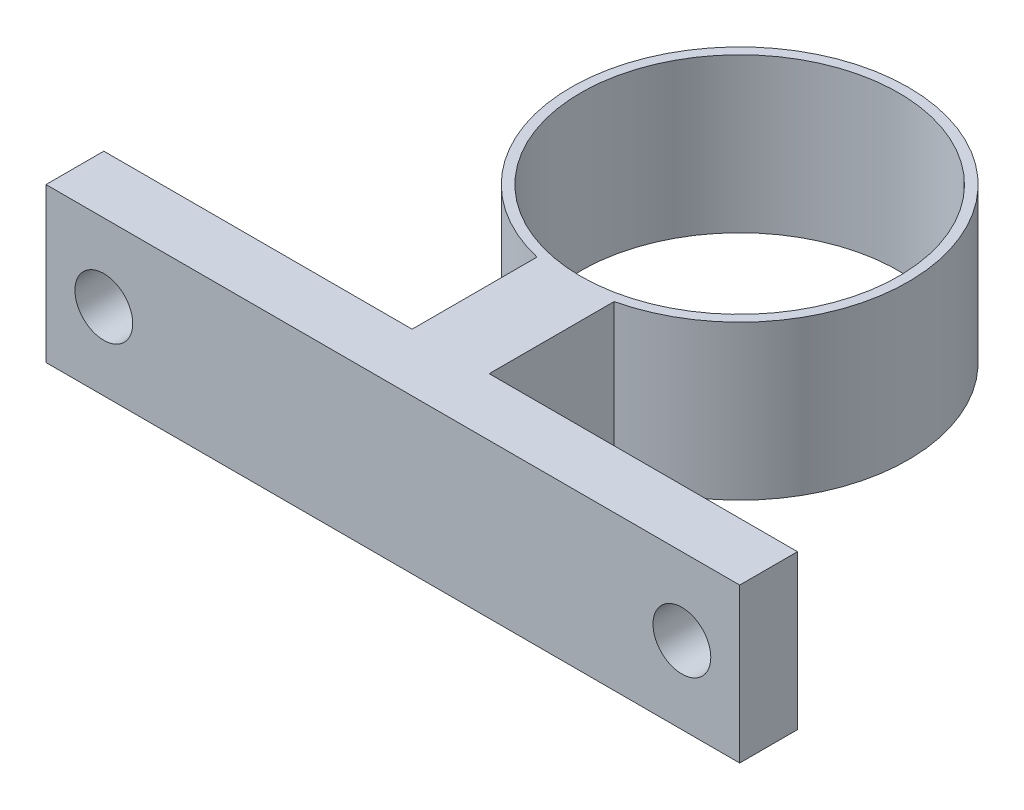
SolidWorks part; units mm, degrees
ref_plane "前视基准面" through (0, 0, 0) normal (0, 0, 1) x (1, 0, 0)
ref_plane "上视基准面" through (0, 0, 0) normal (0, 1, 0) x (1, 0, 0)
ref_plane "右视基准面" through (0, 0, 0) normal (1, 0, 0) x (0, 0, -1)
sketch "草图1" plane through (0, 0, 0) normal (0, 1, 0) x (1, 0, 0)
  circle A0 centre (0, 0) radius 8.25
  circle A1 centre (0, 0) radius 8.75
  dimension "D1" = 16.5
  dimension "D2" = 17.5
extrude "凸台-拉伸2" add sketch "草图1" along normal blind 10
sketch "草图2" plane through (0, 0, 0) normal (0, 1, 0) x (1, 0, 0)
  circle A0 centre (0, 0) radius 8.25
  circle A1 centre (0, 0) radius 2
  dimension "D1" = 4
extrude "凸台-拉伸3" add sketch "草图2" along normal blind 4
sketch "草图3" plane through (0, 0, 0) normal (0, 1, 0) x (1, 0, 0)
  line L0 (-2, 8.5184) -> (2, 8.5184)
  line L1 (-15, 18) -> (-15, 15)
  line L2 (2, 18) -> (15, 18)
  line L3 (-2, 8.5184) -> (-2, 15)
  line L4 (2, 8.5184) -> (2, 15)
  line L5 (-15, 18) -> (-2, 18)
  line L6 (-15, 15) -> (-2, 15)
  line L7 (15, 15) -> (15, 18)
  line L8 (2, 15) -> (15, 15)
  line L9 (2, 18) -> (-2, 18)
  circle A2 centre (0, 0) radius 8.75 construction
  dimension "D1" = 13
  dimension "D2" = 13
  dimension "D3" = 3
  dimension "D4" = 3
extrude "凸台-拉伸4" add sketch "草图3" along normal blind 8
sketch "草图5" plane through (15, 0, 0) normal (1, 0, 0) x (0, 0, -1)
  line L0 (15, 8) -> (18, 8)
  line L1 (15, 8) -> (15, 0)
  line L2 (18, 8) -> (18, 0)
  line L3 (15, 0) -> (18, 0)
  dimension "D1" = 8
extrude "凸台-拉伸5" add sketch "草图5" along normal blind 3
sketch "草图6" plane through (-15, 0, 0) normal (-1, 0, 0) x (0, 0, 1)
  line L0 (-18, 8) -> (-15, 8)
  line L1 (-18, 8) -> (-18, 0)
  line L2 (-15, 8) -> (-15, 0)
  line L3 (-18, 0) -> (-15, 0)
  dimension "D1" = 8
extrude "凸台-拉伸6" add sketch "草图6" along normal blind 3
sketch "草图7" plane through (0, 0, -18) normal (0, 0, -1) x (-1, 0, 0)
  circle A0 centre (-15, 3.754) radius 1.5
  dimension "D2" = 3
extrude "切除-拉伸1" cut sketch "草图7" against normal blind 3
mirror "镜向1" about plane through (0, 0, 0) normal (1, 0, 0) of "切除-拉伸1"
fillet "圆角1" radius 5 2 edges at (2, 4, -8.5184) (-2, 4, -8.5184)
fillet "圆角3" radius 2 2 edges at (-2, 4, -15) (2, 4, -15)
ref_plane "基准面1" through (0, 0, 10) normal (0, 0, 1) x (1, 0, 0)
sketch "草图8" plane through (0, 0, 0) normal (0, 1, 0) x (1, 0, 0)
  circle A0 centre (27.185, 0) radius 8.75
  circle A1 centre (27.185, 0) radius 8.25
  dimension "D1" = 17.5
  dimension "D2" = 16.5
extrude "凸台-拉伸7" add sketch "草图8" along normal blind 8 separate body
sketch "草图9" plane through (0, 0, 0) normal (0, -1, 0) x (1, 0, 0)
  circle A0 centre (27.185, 0) radius 8.25
  circle A1 centre (27.185, 0) radius 6
  dimension "D1" = 12
extrude "凸台-拉伸8" add sketch "草图9" against normal blind 2
sketch "草图10" plane through (0, 0, 0) normal (0, 1, 0) x (1, 0, 0)
  line L1 (27.185, -18) -> (45.185, -18)
  line L2 (27.185, -18) -> (9.185, -18)
  line L3 (9.185, -18) -> (9.185, -14.6639)
  line L4 (9.185, -14.6639) -> (25.185, -14.6639)
  line L5 (45.185, -18) -> (45.185, -14.6639)
  line L6 (45.185, -14.6639) -> (29.185, -14.6639)
  line L7 (25.185, -14.6639) -> (25.185, -8.5184)
  line L8 (25.185, -8.5184) -> (29.185, -8.5184)
  line L9 (29.185, -8.5184) -> (29.185, -14.6639)
  circle A0 centre (27.185, 0) radius 8.75 construction
  dimension "D2" = 18
  dimension "D3" = 18
  dimension "D4" = 16
  dimension "D5" = 16
extrude "凸台-拉伸9" add sketch "草图10" along normal blind 8
sketch "草图11" plane through (0, 0, 18) normal (0, 0, 1) x (1, 0, 0)
  circle A0 centre (12.185, 4) radius 1.5
  circle A1 centre (42.185, 4) radius 1.5
  dimension "D3" = 3
  dimension "D4" = 3
  dimension "D2" = 30
extrude "切除-拉伸2" cut sketch "草图11" against normal blind 8
sketch "草图12" plane through (0, 0, 18) normal (0, 0, 1) x (1, 0, 0)
  line L0 (10.685, 4) -> (10.685, 5)
  line L1 (13.685, 4) -> (13.685, 5)
  line L2 (10.685, 4) -> (10.685, 3)
  line L3 (13.685, 4) -> (13.685, 3)
  circle A0 centre (12.185, 4) radius 1.5 construction
  arc A1 (13.685, 5) -> (10.685, 5) centre (12.185, 5) ccw
  arc A2 (10.685, 3) -> (13.685, 3) centre (12.185, 3) ccw
  dimension "D1" = 1
  dimension "D2" = 1
  dimension "D3" = 1
  dimension "D4" = 1
extrude "切除-拉伸3" cut sketch "草图12" against normal blind 8
sketch "草图13" plane through (0, 0, 18) normal (0, 0, 1) x (1, 0, 0)
  line L0 (40.685, 4) -> (40.685, 5)
  line L2 (43.685, 5) -> (43.685, 4)
  line L3 (43.685, 4) -> (43.685, 3)
  line L5 (40.685, 3) -> (40.685, 4)
  circle A0 centre (42.185, 4) radius 1.5 construction
  arc A1 (43.685, 5) -> (40.685, 5) centre (42.185, 5) ccw
  arc A2 (40.685, 3) -> (43.685, 3) centre (42.185, 3) ccw
  dimension "D1" = 1
  dimension "D2" = 1
  dimension "D3" = 1
extrude "切除-拉伸4" cut sketch "草图13" against normal blind 8
sketch "草图14" plane through (0, 0, 0) normal (0, 1, 0) x (1, 0, 0)
  circle A0 centre (-35.0916, 0) radius 8.75
  circle A1 centre (-35.0916, 0) radius 8.25
  dimension "D1" = 17.5
  dimension "D2" = 16.5
extrude "凸台-拉伸10" add sketch "草图14" along normal blind 8 separate body
sketch "草图15" plane through (0, 0, 0) normal (0, 1, 0) x (1, 0, 0)
  line L0 (-37.0916, -15) -> (-37.0916, -8.5184)
  line L2 (-17.0916, -18) -> (-53.0916, -18)
  line L3 (-53.0916, -18) -> (-53.0916, -15)
  line L4 (-53.0916, -15) -> (-37.0916, -15)
  line L5 (-37.0916, -8.5184) -> (-33.0916, -8.5184)
  line L6 (-33.0916, -15) -> (-17.0916, -15)
  line L7 (-17.0916, -15) -> (-17.0916, -18)
  line L8 (-33.0916, -8.5184) -> (-33.0916, -15)
  circle A0 centre (-35.0916, 0) radius 8.75 construction
  dimension "D4" = 3
  dimension "D5" = 16
  dimension "D6" = 16
extrude "凸台-拉伸11" add sketch "草图15" along normal blind 8
sketch "草图16" plane through (0, 0, 18) normal (0, 0, 1) x (1, 0, 0)
  circle A0 centre (-50.0916, 4) radius 1.5
  circle A1 centre (-20.0916, 4) radius 1.5
  dimension "D3" = 3
  dimension "D4" = 3
extrude "切除-拉伸5" cut sketch "草图16" against normal blind 8
sketch "草图17" plane through (0, 0, 0) normal (0, 1, 0) x (1, 0, 0)
  line L0 (-22.8141, 34.8024) -> (-16.1933, -3.9689)
  line L1 (-16.1933, -3.9689) -> (-7.0267, -18.8252)
  line L2 (-7.0267, -18.8252) -> (52.7145, -30.8366)
  line L3 (52.7145, -30.8366) -> (64.0937, -10)
  line L4 (-5.5, -10) -> (5.5, -10) construction
  line L5 (64.0937, -10) -> (34.2875, 32.086)
  line L6 (34.2875, 32.086) -> (-22.8141, 34.8024)
extrude "切除-拉伸6" cut sketch "草图17" along normal blind 10
